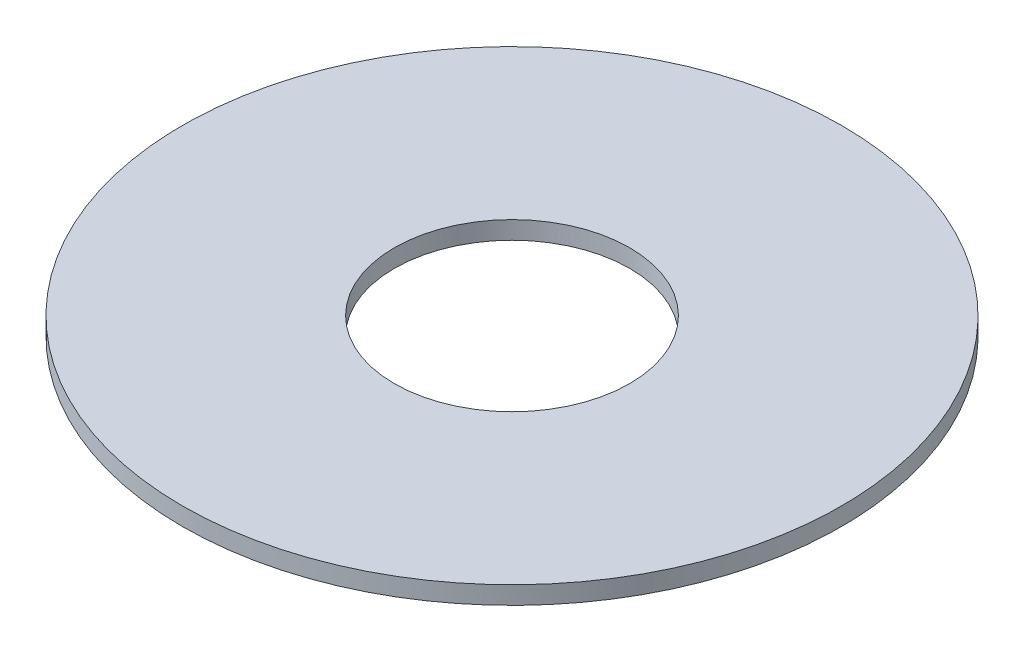
SolidWorks part; units mm, degrees
ref_plane "Front Plane" through (0, 0, 0) normal (0, 0, 1) x (1, 0, 0)
ref_plane "Top Plane" through (0, 0, 0) normal (0, 1, 0) x (1, 0, 0)
ref_plane "Right Plane" through (0, 0, 0) normal (1, 0, 0) x (0, 0, -1)
sketch "Sketch1" plane through (0, 0, 0) normal (0, 1, 0) x (1, 0, 0)
  circle A0 centre (0, 0) radius 12.5
  circle A1 centre (0, 0) radius 35
  dimension "D1" = 25
  dimension "D2" = 70
extrude "Boss-Extrude1" add sketch "Sketch1" along normal blind 1.9
